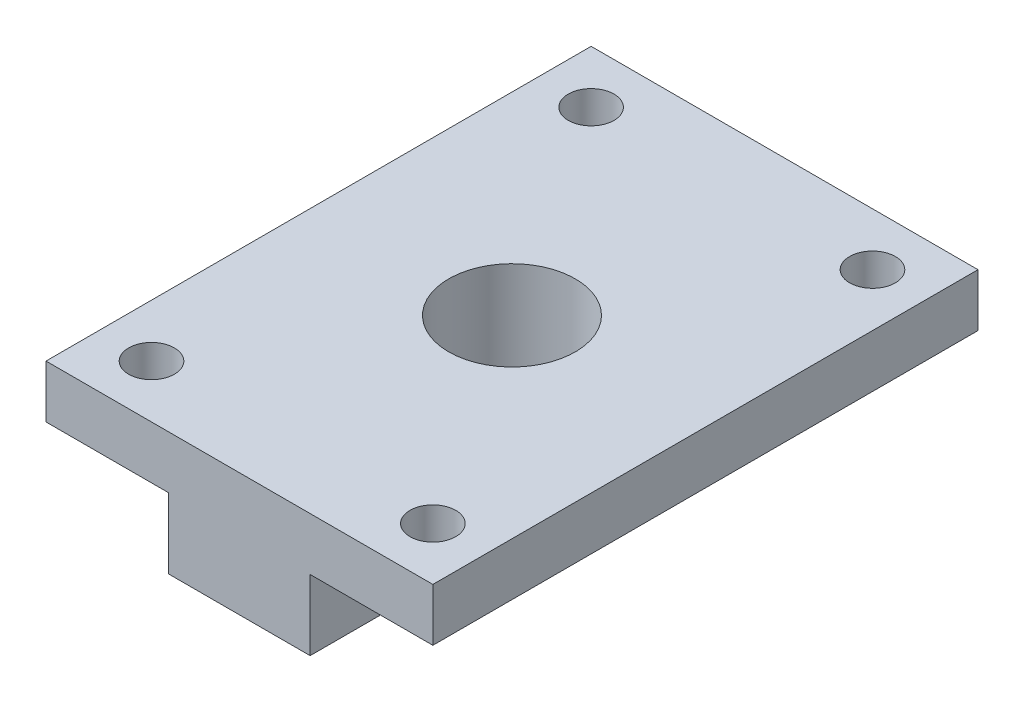
SolidWorks part; units mm, degrees
ref_plane "Front Plane" through (0, 0, 0) normal (0, 0, 1) x (1, 0, 0)
ref_plane "Top Plane" through (0, 0, 0) normal (0, 1, 0) x (1, 0, 0)
ref_plane "Right Plane" through (0, 0, 0) normal (1, 0, 0) x (0, 0, -1)
sketch "Sketch1" plane through (0, 0, 0) normal (0, 1, 0) x (1, 0, 0)
  line L1 (-11, 15.5) -> (11, 15.5)
  line L2 (-11, 15.5) -> (-11, -15.5)
  line L3 (-11, -15.5) -> (11, -15.5)
  line L4 (11, 15.5) -> (11, -15.5)
  circle A0 centre (-8, 12.5) radius 1.3
  circle A1 centre (8, 12.5) radius 1.3
  circle A2 centre (-8, -12.5) radius 1.3
  circle A3 centre (8, -12.5) radius 1.3
  dimension "D5" = 2.6
  dimension "D6" = 3
  dimension "D7" = 3
  dimension "D8" = 2.6
  dimension "D9" = 3
  dimension "D10" = 3
  dimension "D11" = 2.6
  dimension "D12" = 3
  dimension "D14" = 2.6
  dimension "D15" = 3
  dimension "D16" = 3
  dimension "D1" = 22
  dimension "D2" = 31
  dimension "D3" = 11
  dimension "D4" = 15.5
  dimension "D13" = 3
extrude "Boss-Extrude1" add sketch "Sketch1" along normal blind 7
sketch "Sketch2" plane through (0, 7, 0) normal (0, 1, 0) x (1, 0, 0)
  circle A3 centre (0, 0) radius 3.6
  dimension "D1" = 7.2
extrude "Cut-Extrude1" cut sketch "Sketch2" against normal blind 10
sketch "Sketch4" plane through (0, 0, 0) normal (0, -1, 0) x (1, 0, 0)
  line L2 (11, -15.5) -> (11, 15.5)
  line L5 (-11, 15.5) -> (11, 15.5) construction
  line L7 (-11, -15.5) -> (-11, 15.5)
  line L10 (11, -15.5) -> (4.02, -15.5)
  line L12 (11, 15.5) -> (4.02, 15.5)
  line L13 (4.02, -15.5) -> (4.02, 15.5)
  line L15 (-11, -15.5) -> (-4.02, -15.5)
  line L17 (-11, 15.5) -> (-4.02, 15.5)
  line L18 (-4.02, -15.5) -> (-4.02, 15.5)
  dimension "D1" = 6.98
  dimension "D2" = 6.98
extrude "Cut-Extrude2" cut sketch "Sketch4" against normal blind 4
